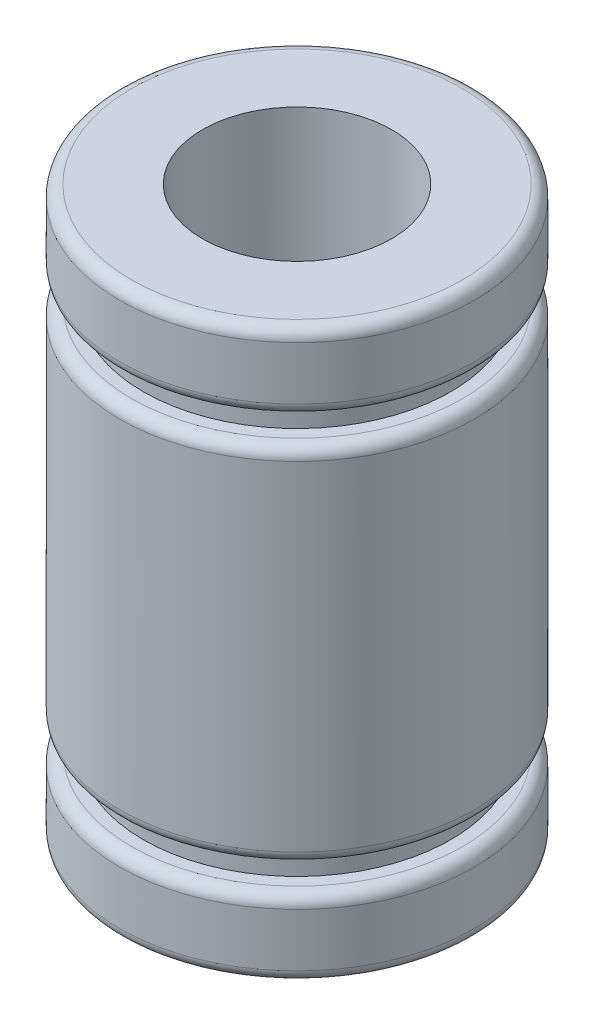
SolidWorks part; units mm, degrees
ref_plane "Front Plane" through (0, 0, 0) normal (0, 0, 1) x (1, 0, 0)
ref_plane "Top Plane" through (0, 0, 0) normal (0, 1, 0) x (1, 0, 0)
ref_plane "Right Plane" through (0, 0, 0) normal (1, 0, 0) x (0, 0, -1)
sketch "Sketch1" plane through (0, 0, 0) normal (1, 0, 0) x (0, 0, -1)
  line L0 (0, 0) -> (0, 24)
  line L1 (0, 24) -> (7.5, 24)
  line L2 (7.5, 24) -> (7.5, 20.75)
  line L3 (7.5, 0) -> (0, 0)
  line L4 (6.5, 24) -> (6.5, 0) construction
  line L5 (6.5, 20.75) -> (7.5, 20.75)
  line L6 (6.5, 19.65) -> (7.5, 19.65)
  line L7 (6.5, 4.35) -> (7.5, 4.35)
  line L8 (6.5, 3.25) -> (7.5, 3.25)
  line L9 (7.5, 3.25) -> (7.5, 0)
  line L10 (7.5, 19.65) -> (7.5, 4.35)
  line L11 (6.5, 20.75) -> (6.5, 19.65)
  line L12 (6.5, 4.35) -> (6.5, 3.25)
  point P7 (6.5, 20.75)
  point P8 (6.5, 19.65)
  point P9 (6.5, 4.35)
  point P10 (6.5, 3.25)
  dimension "D1" = 24
  dimension "D2" = 7.5
  dimension "D3" = 1
  dimension "D4" = 1.1
  dimension "D5" = 1.1
  dimension "D6" = 3.25
  dimension "D7" = 3.25
revolve "Revolve1" add sketch "Sketch1" angle 360 about L0
sketch "Sketch5" plane through (0, 24, 0) normal (0, 1, 0) x (1, 0, 0)
  circle A0 centre (0, 0) radius 4
  dimension "D1" = 8
extrude "Cut-Extrude2" cut sketch "Sketch5" against normal up to next
fillet "Fillet1" radius 0.5 2 edges at (0, 0, -7.5) (0, 24, -7.5)
fillet "Fillet2" radius 0.5 4 edges at (0, 19.65, -7.5) (0, 20.75, -7.5) (0, 4.35, -7.5) (0, 3.25, -7.5)
